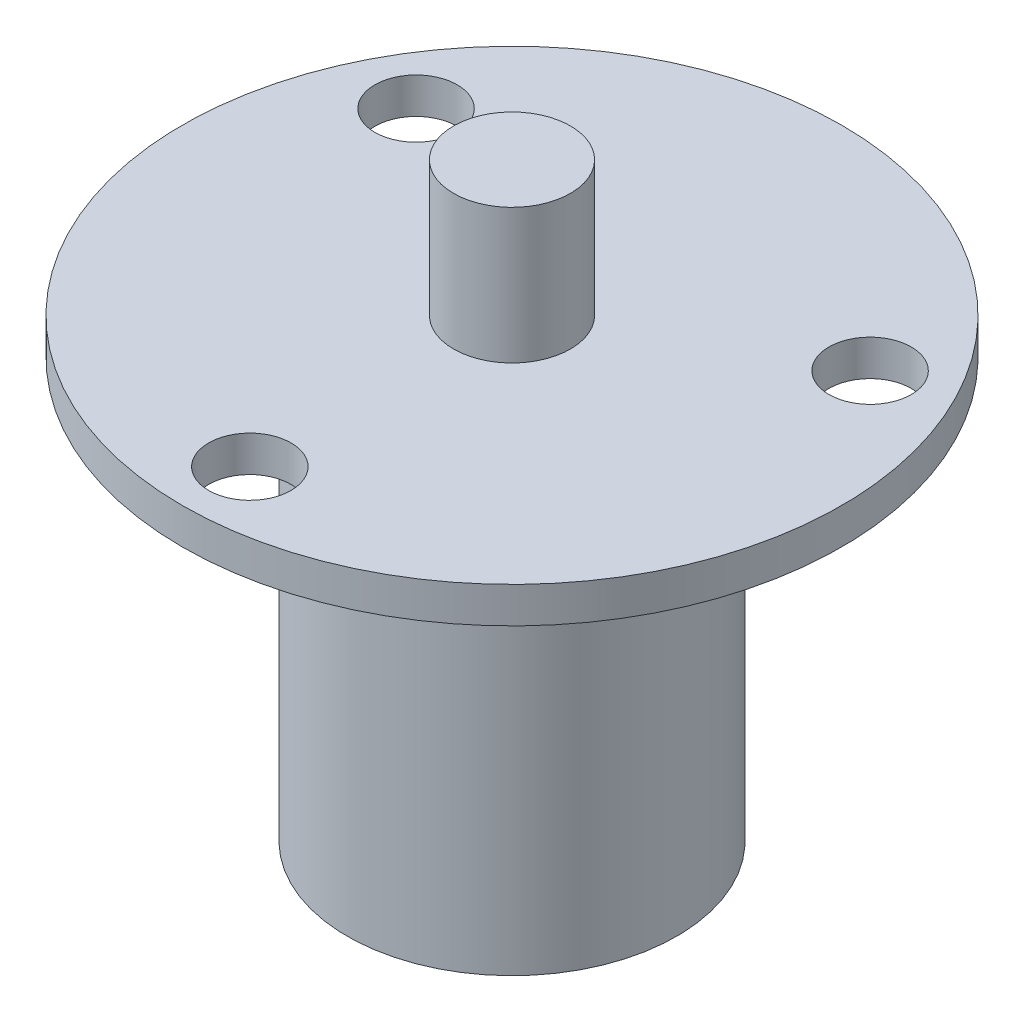
SolidWorks part; units mm, degrees
material "Delrin 2700 NC010, Low Viscosity Acetal Copolymer (SS)"
ref_plane "Front Plane" through (0, 0, 0) normal (0, 0, 1) x (1, 0, 0)
ref_plane "Top Plane" through (0, 0, 0) normal (0, 1, 0) x (1, 0, 0)
ref_plane "Right Plane" through (0, 0, 0) normal (1, 0, 0) x (0, 0, -1)
sketch "Sketch2" plane through (0, 0, 0) normal (0, 1, 0) x (1, 0, 0)
  line L0 (0, 0) -> (-15.1554, 8.75) construction
  line L1 (0, 0) -> (15.1554, 8.75) construction
  line L2 (0, 0) -> (0, -17.5) construction
  circle A0 centre (0, 0) radius 22
  circle A1 centre (0, 0) radius 17.5 construction
  circle A2 centre (15.1554, 8.75) radius 2.75
  circle A3 centre (-15.1554, 8.75) radius 2.75
  circle A4 centre (0, -17.5) radius 2.75
  dimension "D1" = 44
  dimension "D2" = 35
  dimension "D5" = 5.5
  dimension "D3" = 120
  dimension "D4" = 120
extrude "Boss-Extrude1" add sketch "Sketch2" along normal blind 2.4
sketch "Sketch3" plane through (0, 2.4, 0) normal (0, 1, 0) x (1, 0, 0)
  circle A0 centre (0, 0) radius 3.9
  dimension "D1" = 7.8
extrude "Boss-Extrude2" add sketch "Sketch3" along normal blind 9
sketch "Sketch4" plane through (0, 0, 0) normal (0, -1, 0) x (1, 0, 0)
  circle A0 centre (0, 0) radius 11
  dimension "D1" = 22
extrude "Boss-Extrude3" add sketch "Sketch4" along normal blind 28
